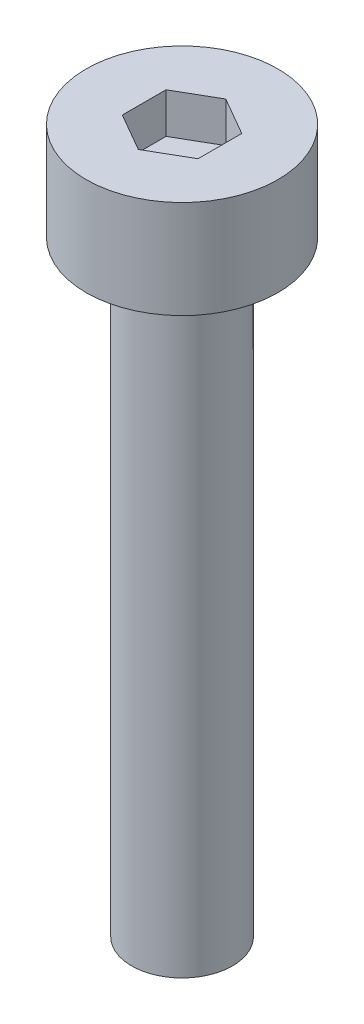
SolidWorks part; units mm, degrees
ref_plane "Front Plane" through (0, 0, 0) normal (0, 0, 1) x (1, 0, 0)
ref_plane "Top Plane" through (0, 0, 0) normal (0, 1, 0) x (1, 0, 0)
ref_plane "Right Plane" through (0, 0, 0) normal (1, 0, 0) x (0, 0, -1)
sketch "Sketch1" plane through (0, 0, 0) normal (0, 1, 0) x (1, 0, 0)
  circle A0 centre (0, 0) radius 1.9
  dimension "D1" = 3.8
extrude "Boss-Extrude1" add sketch "Sketch1" along normal blind 1.94
sketch "Sketch2" plane through (0, 1.94, 0) normal (0, 1, 0) x (1, 0, 0)
  line L1 (0, 0.866) -> (-0.75, 0.433)
  line L2 (-0.75, 0.433) -> (-0.75, -0.433)
  line L3 (-0.75, -0.433) -> (0, -0.866)
  line L4 (0, -0.866) -> (0.75, -0.433)
  line L5 (0.75, -0.433) -> (0.75, 0.433)
  line L6 (0.75, 0.433) -> (0, 0.866)
  circle A0 centre (0, 0) radius 0.75 construction
  dimension "D1" = 1.5
extrude "Cut-Extrude1" cut sketch "Sketch2" against normal blind 0.8
sketch "Sketch3" plane through (0, 0, 0) normal (0, -1, 0) x (1, 0, 0)
  circle A0 centre (0, 0) radius 1
  dimension "D1" = 2
extrude "Boss-Extrude2" add sketch "Sketch3" along normal blind 12
